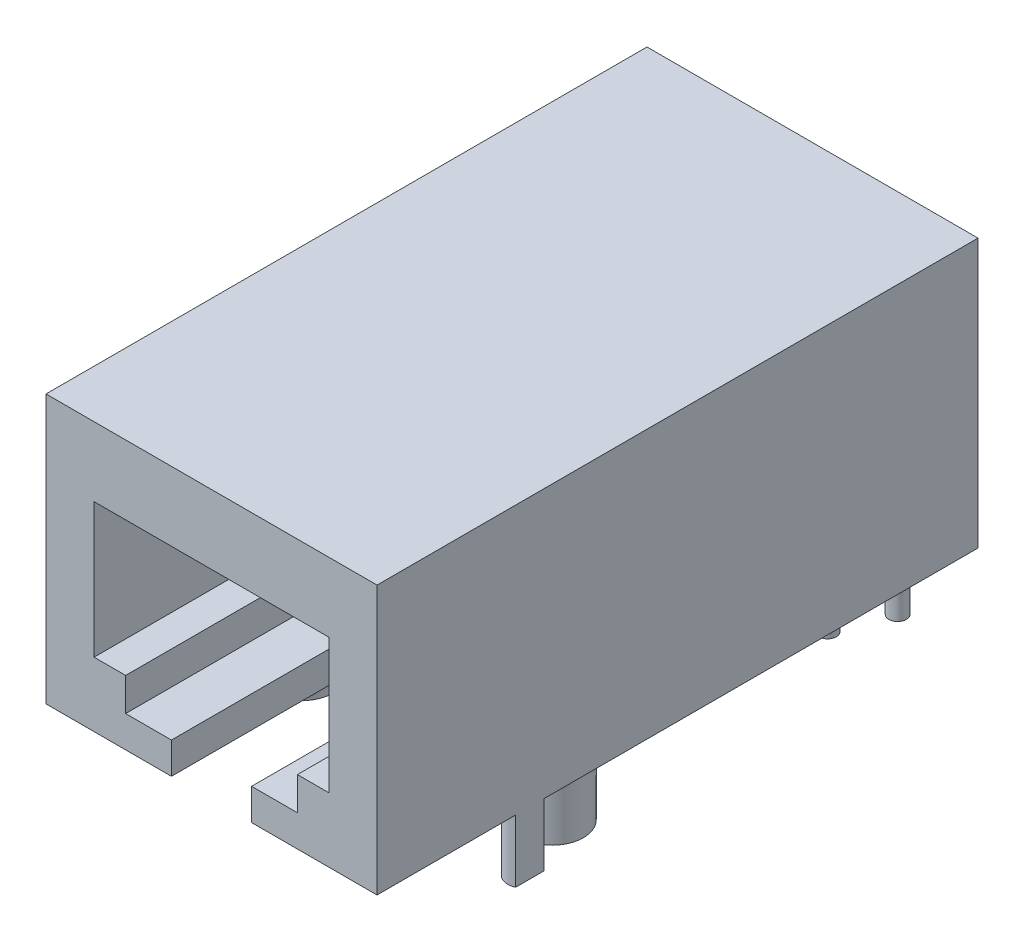
SolidWorks part; units mm, degrees
ref_plane "Front Plane" through (0, 0, 0) normal (0, 0, 1) x (1, 0, 0)
ref_plane "Top Plane" through (0, 0, 0) normal (0, 1, 0) x (1, 0, 0)
ref_plane "Right Plane" through (0, 0, 0) normal (1, 0, 0) x (0, 0, -1)
sketch "Sketch1" plane through (0, 0, 0) normal (0, 1, 0) x (1, 0, 0)
  line L1 (0, 0) -> (16.7894, 0)
  line L2 (0, 0) -> (0, 30.48)
  line L3 (0, 30.48) -> (16.7894, 30.48)
  line L4 (16.7894, 0) -> (16.7894, 30.48)
  dimension "D1" = 16.7894
  dimension "D2" = 30.48
extrude "Boss-Extrude1" add sketch "Sketch1" along normal blind 13.6144
sketch "Sketch4" plane through (0, 0, 0) normal (0, 0, 1) x (1, 0, 0)
  line L0 (2.4384, 10.1036) -> (14.351, 10.1036)
  line L1 (14.351, 10.1036) -> (14.351, 3.271)
  line L2 (14.351, 3.271) -> (12.7508, 3.271)
  line L3 (12.7508, 3.271) -> (12.7508, 1.5946)
  line L4 (12.7508, 1.5946) -> (10.4267, 1.5946)
  line L5 (10.4267, 1.5946) -> (10.4267, 0)
  line L6 (10.4267, 0) -> (6.3627, 0)
  line L7 (6.3627, 0) -> (6.3627, 1.5946)
  line L8 (6.3627, 1.5946) -> (4.0386, 1.5946)
  line L9 (4.0386, 1.5946) -> (4.0386, 3.271)
  line L10 (4.0386, 3.271) -> (2.4384, 3.271)
  line L11 (2.4384, 3.271) -> (2.4384, 10.1036)
  line L12 (0, 0) -> (16.7894, 0) construction
  point P14 (8.3947, 0)
  point P15 (8.3947, 0)
  point P16 (2.4384, 10.1036)
  dimension "D1" = 11.9126
  dimension "D2" = 8.509
  dimension "D3" = 6.8326
  dimension "D4" = 1.5946
  dimension "D6" = 4.064
  dimension "D7" = 8.7122
extrude "Cut-Extrude1" cut sketch "Sketch4" against normal blind 17.78
sketch "Sketch8" plane through (0, 0, 0) normal (0, -1, 0) x (1, 0, 0)
  line L2 (0, -30.48) -> (0, 0) construction
  line L4 (0, 0) -> (6.3627, 0) construction
  circle A0 centre (0.3302, -7.747) radius 0.7874
  circle A1 centre (16.4592, -7.747) radius 0.7874
  circle A2 centre (2.0447, -10.922) radius 1.5875
  circle A3 centre (14.7447, -10.922) radius 1.5875
  circle A4 centre (6.3627, -28.702) radius 0.4445
  circle A5 centre (3.3147, -26.162) radius 0.4445
  circle A6 centre (4.3307, -28.702) radius 0.4445
  circle A7 centre (5.3467, -26.162) radius 0.4445
  circle A8 centre (11.4427, -26.162) radius 0.4445
  circle A9 centre (13.4747, -26.162) radius 0.4445
  circle A10 centre (10.4267, -28.702) radius 0.4445
  circle A11 centre (12.4587, -28.702) radius 0.4445
  circle A12 centre (14.4907, -28.702) radius 0.4445
  point P30 (0, 0)
  point P31 (0, 0)
  dimension "D1" = 3.175
  dimension "D2" = 1.5748
  dimension "D7" = 0.3302
  dimension "D11" = 0.889
  dimension "D12" = 2.032
  dimension "D3" = 16.129
  dimension "D4" = 12.7
  dimension "D5" = 1.7145
  dimension "D6" = 1.7145
  dimension "D8" = 7.747
  dimension "D9" = 3.175
  dimension "D10" = 3.175
  dimension "D13" = 4.064
  dimension "D14" = 2.032
  dimension "D15" = 2.032
  dimension "D16" = 1.016
  dimension "D17" = 2.032
  dimension "D18" = 6.096
  dimension "D19" = 2.032
  dimension "D20" = 18.415
  dimension "D21" = 2.54
  dimension "D22" = 1.27
extrude "Boss-Extrude3" add sketch "Sketch8" along normal blind 3.175
sketch "Sketch9" plane through (0, 10.1036, 0) normal (0, -1, 0) x (1, 0, 0)
  line L0 (12.6802, -17.78) -> (12.6802, -11.43)
  line L1 (12.6802, -11.43) -> (12.1102, -11.43)
  line L2 (12.1102, -11.43) -> (12.1102, -17.78)
  line L3 (12.1102, -17.78) -> (12.6802, -17.78)
  line L4 (11.5372, -17.78) -> (11.5372, -11.43)
  line L5 (11.5372, -11.43) -> (10.9672, -11.43)
  line L6 (10.9672, -11.43) -> (10.9672, -17.78)
  line L7 (10.9672, -17.78) -> (11.5372, -17.78)
  line L8 (10.3942, -17.78) -> (10.3942, -11.43)
  line L9 (10.3942, -11.43) -> (9.8242, -11.43)
  line L10 (9.8242, -11.43) -> (9.8242, -17.78)
  line L11 (9.8242, -17.78) -> (10.3942, -17.78)
  line L12 (9.2512, -17.78) -> (9.2512, -11.43)
  line L13 (9.2512, -11.43) -> (8.6812, -11.43)
  line L14 (8.6812, -11.43) -> (8.6812, -17.78)
  line L15 (8.6812, -17.78) -> (9.2512, -17.78)
  line L16 (8.1082, -17.78) -> (8.1082, -11.43)
  line L17 (8.1082, -11.43) -> (7.5382, -11.43)
  line L18 (7.5382, -11.43) -> (7.5382, -17.78)
  line L19 (7.5382, -17.78) -> (8.1082, -17.78)
  line L20 (6.9652, -17.78) -> (6.9652, -11.43)
  line L21 (6.9652, -11.43) -> (6.3952, -11.43)
  line L22 (6.3952, -11.43) -> (6.3952, -17.78)
  line L23 (6.3952, -17.78) -> (6.9652, -17.78)
  line L24 (5.8222, -17.78) -> (5.8222, -11.43)
  line L25 (5.8222, -11.43) -> (5.2522, -11.43)
  line L26 (5.2522, -11.43) -> (5.2522, -17.78)
  line L27 (5.2522, -17.78) -> (5.8222, -17.78)
  line L28 (4.6792, -17.78) -> (4.6792, -11.43)
  line L29 (4.6792, -11.43) -> (4.1092, -11.43)
  line L30 (4.1092, -11.43) -> (4.1092, -17.78)
  line L31 (4.1092, -17.78) -> (4.6792, -17.78)
  line L33 (12.6802, -11.43) -> (4.1092, -11.43) construction
  line L34 (12.6802, -11.43) -> (12.6802, -17.78) construction
  line L35 (12.6802, -17.78) -> (4.1092, -17.78) construction
  line L36 (4.1092, -11.43) -> (4.1092, -17.78) construction
  line L38 (14.351, -17.78) -> (2.4384, -17.78) construction
  point P4 (8.3947, -17.78)
  point P35 (8.3947, -17.78)
  dimension "D1" = 6.35
  dimension "D2" = 0.57
  dimension "D3" = 8
extrude "Boss-Extrude4" add sketch "Sketch9" along normal blind 1.27
sketch "Sketch10" plane through (0, 0, -17.78) normal (0, 0, 1) x (1, 0, 0)
  line L0 (10.4267, 0) -> (10.4267, 1.5946) construction
  line L1 (10.4267, 0) -> (6.3627, 0)
  line L2 (10.4267, 0) -> (10.4267, 5.08)
  line L3 (10.4267, 5.08) -> (6.3627, 5.08)
  line L4 (6.3627, 0) -> (6.3627, 5.08)
  line L5 (6.3627, 0) -> (10.4267, 0) construction
  dimension "D1" = 5.08
extrude "Cut-Extrude2" cut sketch "Sketch10" against normal blind 1.27
sketch "Sketch11" plane through (0, 0, -19.05) normal (0, 0, 1) x (1, 0, 0)
  line L0 (6.3627, 3.048) -> (10.4267, 3.048) construction
  line L1 (6.3627, 5.08) -> (6.3627, 0) construction
  line L2 (10.4267, 0) -> (10.4267, 5.08) construction
  line L3 (6.3627, 0) -> (10.4267, 0) construction
  text T0 "bel" font "Century Gothic" height in points 6
  dimension "D1" = 3.048
extrude "Boss-Extrude5" add sketch "Sketch11" along normal blind 1.27
sketch "Sketch12" plane through (0, 0, 0) normal (0, 1, 0) x (1, 0, 0)
  line L1 (0, 8.4618) -> (-0.9046, 8.4618)
  line L2 (0, 8.4618) -> (0, 7.0322)
  line L3 (0, 7.0322) -> (-0.9046, 7.0322)
  line L4 (-0.9046, 8.4618) -> (-0.9046, 7.0322)
extrude "Cut-Extrude3" cut sketch "Sketch12" against normal blind 25.4
sketch "Sketch13" plane through (0, 0, 0) normal (0, 1, 0) x (1, 0, 0)
  line L1 (16.7894, 7.0322) -> (18.0573, 7.0322)
  line L2 (16.7894, 7.0322) -> (16.7894, 8.4618)
  line L3 (16.7894, 8.4618) -> (18.0573, 8.4618)
  line L4 (18.0573, 7.0322) -> (18.0573, 8.4618)
extrude "Cut-Extrude4" cut sketch "Sketch13" against normal blind 25.4
sketch "Sketch14" plane through (0, -3.175, 0) normal (0, -1, 0) x (1, 0, 0)
  circle A0 centre (2.0447, -10.922) radius 0.635
  dimension "D1" = 1.27
extrude "Cut-Extrude5" cut sketch "Sketch14" against normal blind 2.54
sketch "Sketch15" plane through (0, -3.175, 0) normal (0, -1, 0) x (1, 0, 0)
  circle A0 centre (14.7447, -10.922) radius 0.635
  dimension "D1" = 1.27
extrude "Cut-Extrude6" cut sketch "Sketch15" against normal blind 2.54
